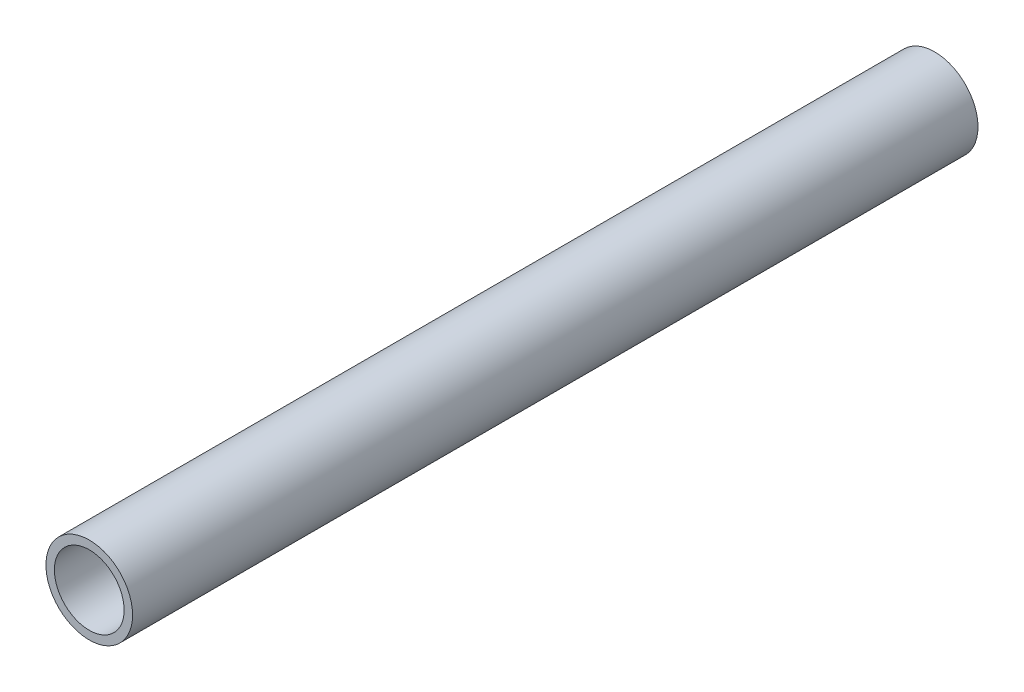
SolidWorks part; units mm, degrees
ref_plane "Front Plane" through (0, 0, 0) normal (0, 0, 1) x (1, 0, 0)
ref_plane "Top Plane" through (0, 0, 0) normal (0, 1, 0) x (1, 0, 0)
ref_plane "Right Plane" through (0, 0, 0) normal (1, 0, 0) x (0, 0, -1)
sketch "Sketch1" plane through (0, 0, 0) normal (0, 0, 1) x (1, 0, 0)
  circle A0 centre (0, 0) radius 10.25
  circle A1 centre (0, 0) radius 8.25
  dimension "D1" = 20.5
  dimension "D2" = 2
extrude "Boss-Extrude1" add sketch "Sketch1" along normal blind 200
